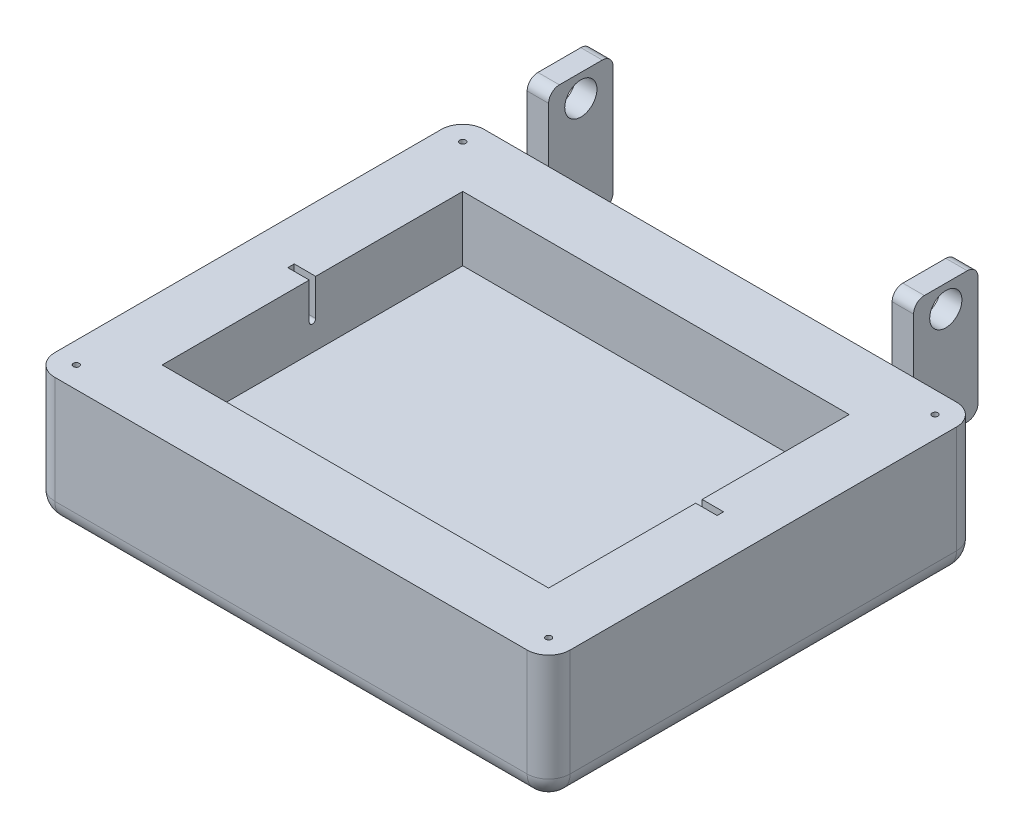
SolidWorks part; units mm, degrees
ref_plane "Front Plane" through (0, 0, 0) normal (0, 0, 1) x (1, 0, 0)
ref_plane "Top Plane" through (0, 0, 0) normal (0, 1, 0) x (1, 0, 0)
ref_plane "Right Plane" through (0, 0, 0) normal (1, 0, 0) x (0, 0, -1)
sketch "Sketch4" plane through (0, 0, 0) normal (0, 1, 0) x (1, 0, 0)
  line L1 (-152.4, -127) -> (152.4, -127)
  line L2 (-152.4, -127) -> (-152.4, 127)
  line L3 (-152.4, 127) -> (152.4, 127)
  line L4 (152.4, -127) -> (152.4, 127)
  line L5 (-152.4, -127) -> (152.4, 127) construction
  line L6 (-152.4, 127) -> (152.4, -127) construction
  point P0 (0, 0)
  dimension "D1" = 254
  dimension "D2" = 304.8
extrude "Boss-Extrude1" add sketch "Sketch4" along normal blind 76.2
sketch "Sketch5" plane through (0, 76.2, 0) normal (0, 1, 0) x (1, 0, 0)
  line L1 (-114.3, -88.9) -> (114.3, -88.9)
  line L2 (-114.3, -88.9) -> (-114.3, 88.9)
  line L3 (-114.3, 88.9) -> (114.3, 88.9)
  line L4 (114.3, -88.9) -> (114.3, 88.9)
  line L5 (-114.3, -88.9) -> (114.3, 88.9) construction
  line L6 (-114.3, 88.9) -> (114.3, -88.9) construction
  point P0 (0, 0)
  dimension "D1" = 228.6
  dimension "D2" = 177.8
extrude "Cut-Extrude1" cut sketch "Sketch5" against normal blind 38.1
sketch "Sketch8" plane through (0, 76.2, 0) normal (0, 1, 0) x (1, 0, 0)
  line L0 (-152.4, -127) -> (152.4, -127) construction
  line L1 (-152.4, 127) -> (-152.4, -127) construction
  line L2 (152.4, -127) -> (152.4, 127) construction
  line L3 (152.4, 127) -> (-152.4, 127) construction
  circle A0 centre (-139.7, 114.3) radius 6.35
  circle A1 centre (139.7, 114.3) radius 6.35
  circle A2 centre (139.7, -114.3) radius 6.35
  circle A3 centre (-139.7, -114.3) radius 6.35
  dimension "D1" = 12.7
  dimension "D2" = 12.7
  dimension "D3" = 12.7
  dimension "D4" = 12.7
  dimension "D7" = 12.7
  dimension "D8" = 12.7
  dimension "D9" = 12.7
  dimension "D10" = 12.7
  dimension "D11" = 12.7
  dimension "D5" = 12.7
  dimension "D6" = 12.7
  dimension "D12" = 12.7
fillet "Fillet1" radius 12.7 8 edges at (152.4, 38.1, 127) (152.4, 0, 0) (0, 0, -127) (152.4, 38.1, -127) (-152.4, 38.1, -127) (-152.4, 0, 0) (0, 0, 127) (-152.4, 38.1, 127)
sketch "Sketch11" plane through (0, 76.2, 0) normal (0, 1, 0) x (1, 0, 0)
  line L0 (139.7, 127) -> (-139.7, 127) construction
  line L1 (-114.3, 127) -> (-101.6, 127)
  line L2 (-114.3, 127) -> (-114.3, 165.1)
  line L3 (-114.3, 165.1) -> (-101.6, 165.1)
  line L4 (-101.6, 127) -> (-101.6, 165.1)
  line L5 (152.4, -114.3) -> (152.4, 114.3) construction
  line L6 (114.3, 127) -> (101.6, 127)
  line L7 (114.3, 127) -> (114.3, 165.1)
  line L8 (114.3, 165.1) -> (101.6, 165.1)
  line L9 (101.6, 127) -> (101.6, 165.1)
  line L10 (-152.4, 114.3) -> (-152.4, -114.3) construction
  point P10 (-114.3, 146.05)
  dimension "D1" = 12.7
  dimension "D2" = 12.7
  dimension "D3" = 38.1
  dimension "D4" = 38.1
  dimension "D5" = 38.1
  dimension "D6" = 50.8
extrude "Boss-Extrude2" add sketch "Sketch11" along normal mid plane 77.47
sketch "Sketch12" plane through (-114.3, 0, 0) normal (-1, 0, 0) x (0, 0, 1)
  line L2 (-127, 114.935) -> (-127, 76.2) construction
  line L3 (-114.3, 76.2) -> (114.3, 76.2) construction
  circle A0 centre (-146.05, 101.6) radius 9.525
  dimension "D1" = 19.05
  dimension "D2" = 19.05
  dimension "D3" = 25.4
extrude "Cut-Extrude4" cut sketch "Sketch12" against normal through all
fillet "Fillet3" radius 6.35 2 edges at (-107.95, 114.935, -127) (107.95, 114.935, -127)
sketch "Sketch13" plane through (0, 76.2, 0) normal (0, 1, 0) x (1, 0, 0)
  line L1 (-127, 1.905) -> (127, 1.905)
  line L2 (-127, 1.905) -> (-127, -1.905)
  line L3 (-127, -1.905) -> (127, -1.905)
  line L4 (127, 1.905) -> (127, -1.905)
  dimension "D1" = 3.81
  dimension "D2" = 254
  dimension "D3" = 127
  dimension "D4" = 1.905
extrude "Cut-Extrude5" cut sketch "Sketch13" against normal blind 23.495
sketch "Sketch18" plane through (-127, 0, 0) normal (1, 0, 0) x (0, 0, -1)
  line L0 (1.905, 54.61) -> (1.905, 52.705)
  line L1 (1.905, 52.705) -> (-1.905, 52.705)
  line L2 (-1.905, 52.705) -> (-1.905, 54.61)
  line L3 (-1.905, 52.705) -> (1.905, 52.705) construction
  line L4 (1.905, 52.705) -> (1.905, 76.2) construction
  arc A0 (-1.905, 54.61) -> (1.905, 54.61) centre (0, 54.61) ccw
  line M3 (-1.905, 76.2) -> (-1.905, 52.705)
  line M4 (-1.905, 52.705) -> (1.905, 52.705)
  line M5 (1.905, 52.705) -> (1.905, 76.2)
  dimension "D2" = 1.905
  dimension "D1" = 1.905
extrude "Boss-Extrude3" add sketch "Sketch18" along normal blind 12.7 contours A0 M3 M4 | A0 L1 M5
mirror "Mirror1" about plane through (0, 0, 0) normal (1, 0, 0) of "Boss-Extrude3"
fillet "Fillet5" radius 6.35 4 edges at (107.95, 114.935, -165.1) (107.95, 37.465, -165.1) (-107.95, 37.465, -165.1) (-107.95, 114.935, -165.1)
hole_wizard "#8-32 Tapped Hole1" positions "Sketch19" profile "Sketch20" tap size "#8-32" standard "ANSI Inch"
sketch "Sketch19" plane through (0, 76.2, 0) normal (0, 1, 0) x (1, 0, 0)
  point P0 (-139.7, -114.3)
  point P3 (-139.7, 114.3)
  point P6 (139.7, 114.3)
  point P9 (139.7, -114.3)
sketch "Sketch20" plane through (-139.7, 76.2, 114.3) normal (1, 0, 0) x (0, 0, 1)
  line L0 (0, 0) -> (0, 10.6898)
  line L1 (0, 10.6898) -> (1.7272, 9.652)
  line L2 (1.7272, 9.652) -> (1.7272, 0)
  line L5 (1.7272, 0) -> (0, 0)
  line L10 (0, 10.6898) -> (-1.7272, 9.652) construction
  line L11 (0, -6.35) -> (0, 107.95) construction
  dimension "Tap Drill Dia." = 3.4544
  dimension "Tap Drill Depth" = 9.652
  dimension "Drill Angle" = 118
cosmetic thread "Hole Thread1" parameters "D1"=8.382, "D2"=4.1656
cosmetic thread "Hole Thread2" parameters "D1"=8.382, "D2"=4.1656
cosmetic thread "Hole Thread3" parameters "D1"=8.382, "D2"=4.1656
cosmetic thread "Hole Thread4" parameters "D1"=8.382, "D2"=4.1656
